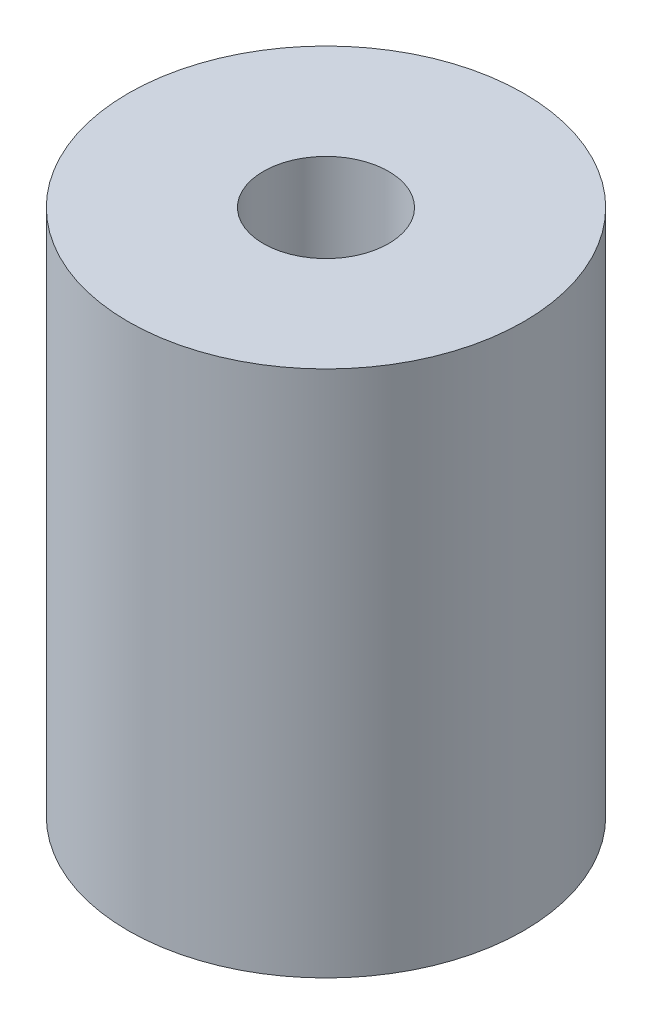
SolidWorks part; units mm, degrees
ref_plane "Front Plane" through (0, 0, 0) normal (0, 0, 1) x (1, 0, 0)
ref_plane "Top Plane" through (0, 0, 0) normal (0, 1, 0) x (1, 0, 0)
ref_plane "Right Plane" through (0, 0, 0) normal (1, 0, 0) x (0, 0, -1)
sketch "Sketch1" plane through (0, 0, 0) normal (0, 1, 0) x (1, 0, 0)
  circle A0 centre (0, 0) radius 7.5
  dimension "D1" = 15
extrude "Boss-Extrude1" add sketch "Sketch1" along normal mid plane 20
sketch "Sketch2" plane through (0, 10, 0) normal (0, 1, 0) x (1, 0, 0)
  circle A0 centre (0, 0) radius 2.375
  dimension "D1" = 4.75
extrude "Cut-Extrude1" cut sketch "Sketch2" against normal blind 9
sketch "Sketch3" plane through (0, -10, 0) normal (0, -1, 0) x (1, 0, 0)
  circle A0 centre (0, 0) radius 2.375
  dimension "D1" = 4.75
extrude "Cut-Extrude2" cut sketch "Sketch3" against normal blind 9
